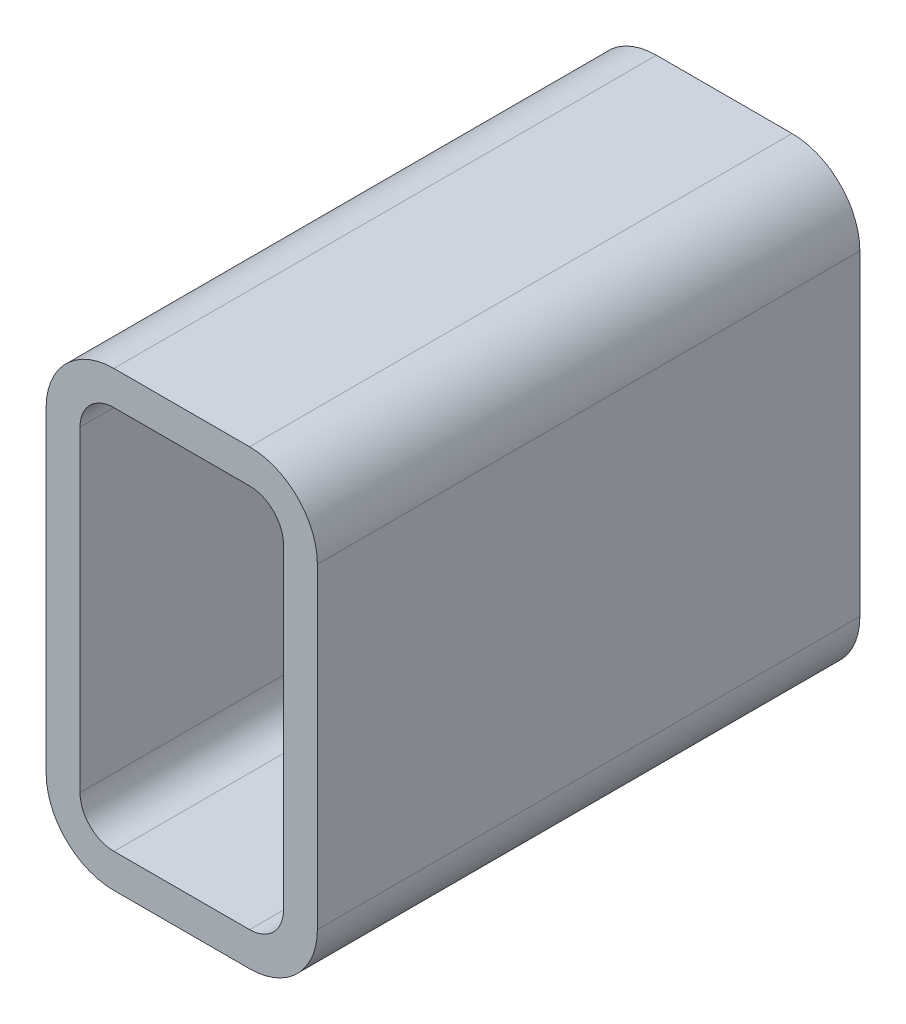
SolidWorks part; units mm, degrees
ref_plane "Plane1" through (0, 0, 0) normal (0, 0, 1) x (1, 0, 0)
ref_plane "Plane2" through (0, 0, 0) normal (0, 1, 0) x (1, 0, 0)
ref_plane "Plane3" through (0, 0, 0) normal (1, 0, 0) x (0, 0, -1)
sketch "Sketch1" plane through (0, 0, 0) normal (0, 0, 1) x (1, 0, 0)
  line L0 (19.05, 9.525) -> (57.15, 9.525)
  line L1 (9.525, 19.05) -> (9.525, 107.95)
  line L2 (57.15, 117.475) -> (19.05, 117.475)
  line L3 (66.675, 107.95) -> (66.675, 19.05)
  line L4 (19.05, 0) -> (57.15, 0)
  line L5 (0, 19.05) -> (0, 107.95)
  line L6 (57.15, 127) -> (19.05, 127)
  line L7 (76.2, 107.95) -> (76.2, 19.05)
  arc A0 (76.2, 107.95) -> (57.15, 127) centre (57.15, 107.95) ccw
  arc A1 (57.15, 0) -> (76.2, 19.05) centre (57.15, 19.05) ccw
  arc A2 (0, 19.05) -> (19.05, 0) centre (19.05, 19.05) ccw
  arc A3 (19.05, 127) -> (0, 107.95) centre (19.05, 107.95) ccw
  arc A4 (19.05, 117.475) -> (9.525, 107.95) centre (19.05, 107.95) ccw
  arc A5 (66.675, 107.95) -> (57.15, 117.475) centre (57.15, 107.95) ccw
  arc A6 (57.15, 9.525) -> (66.675, 19.05) centre (57.15, 19.05) ccw
  arc A7 (9.525, 19.05) -> (19.05, 9.525) centre (19.05, 19.05) ccw
  dimension "D1" = 19.05
  dimension "Thickness" = 9.525
  dimension "V_leg" = 127
  dimension "H_leg" = 76.2
extrude "BaseTubeR" add sketch "Sketch1" along normal mid plane 152.4
sketch "Sketch2" plane through (0, 0, 0) normal (-1, 0, 0) x (0, 0, 1)
  line L0 (-76.2, 107.95) -> (-76.2, 19.05) construction
  line L1 (76.2, 19.05) -> (-76.2, 19.05) construction
  circle A0 centre (-38.1, 31.75) radius 9.525
  dimension "D1" = 19.05
  dimension "D3" = 12.7
  dimension "D2" = 38.1
extrude "Cut-Extrude1" cut sketch "Sketch2" against normal up to next
equation "\"D1@Sketch1\" = \"Thickness@Sketch1\" * 2"
